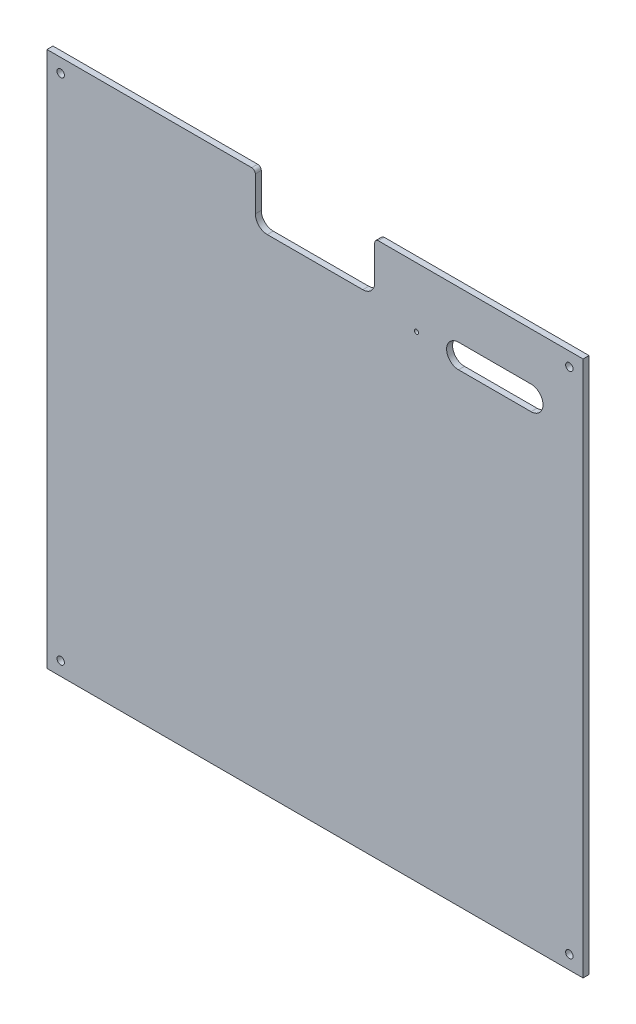
SolidWorks part; units mm, degrees
material "ABS PC"
ref_plane "Piano frontale" through (0, 0, 0) normal (0, 0, 1) x (1, 0, 0)
ref_plane "Piano superiore" through (0, 0, 0) normal (0, 1, 0) x (1, 0, 0)
ref_plane "Piano destro" through (0, 0, 0) normal (1, 0, 0) x (0, 0, -1)
sketch "Schizzo1" plane through (0, 0, 0) normal (0, 0, 1) x (1, 0, 0)
  line L0 (0, 0) -> (0, 449)
  line L1 (0, 449) -> (171.5, 449)
  line L2 (449, 449) -> (449, 0)
  line L3 (449, 0) -> (0, 0)
  line L4 (174.5, 446) -> (174.5, 417)
  line L5 (184.5, 407) -> (264.5, 407)
  line L6 (274.5, 417) -> (274.5, 446)
  line L7 (277.5, 449) -> (449, 449)
  line L8 (154.5, 399) -> (294.5, 399) construction
  line L9 (224.5, 379) -> (224.5, 419) construction
  line L10 (344.7159, 399) -> (405.4404, 399) construction
  line L11 (344.7159, 409) -> (405.4404, 409)
  line L12 (344.7159, 389) -> (405.4404, 389)
  line L13 (0, 224.5) -> (449, 224.5) construction
  line L23 (73.9219, 399) -> (73.9219, 449) construction
  line L24 (174.5, 431.5) -> (314.5, 431.5) construction
  arc A0 (174.5, 417) -> (184.5, 407) centre (184.5, 417) ccw
  arc A1 (274.5, 417) -> (264.5, 407) centre (264.5, 417) cw
  circle A2 centre (11.5, 11.5) radius 3.1
  circle A3 centre (437.5, 11.5) radius 3.1
  circle A4 centre (437.5, 437.5) radius 3.1
  circle A5 centre (11.5, 437.5) radius 3.1
  circle A6 centre (309.5, 399) radius 1.75
  arc A7 (277.5, 449) -> (274.5, 446) centre (277.5, 446) ccw
  arc A8 (344.7159, 409) -> (344.7159, 389) centre (344.7159, 399) ccw
  arc A9 (405.4404, 389) -> (405.4404, 409) centre (405.4404, 399) ccw
  arc A10 (174.5, 446) -> (171.5, 449) centre (171.5, 446) ccw
  point P11 (174.5, 407)
  point P14 (274.5, 407)
  point P33 (375.0781, 399)
  point P44 (174.5, 449)
  dimension "D5" = 10
  dimension "D6" = 11.5
  dimension "D7" = 11.5
  dimension "D8" = 6.2
  dimension "D9" = 3.5
  dimension "D10" = 35
  dimension "D12" = 3
  dimension "D1" = 449
  dimension "D2" = 449
  dimension "D3" = 100
  dimension "D4" = 42
  dimension "D11" = 20
  dimension "D21" = 50
extrude "Estrusione-Estrusione1" add sketch "Schizzo1" along normal blind 5
